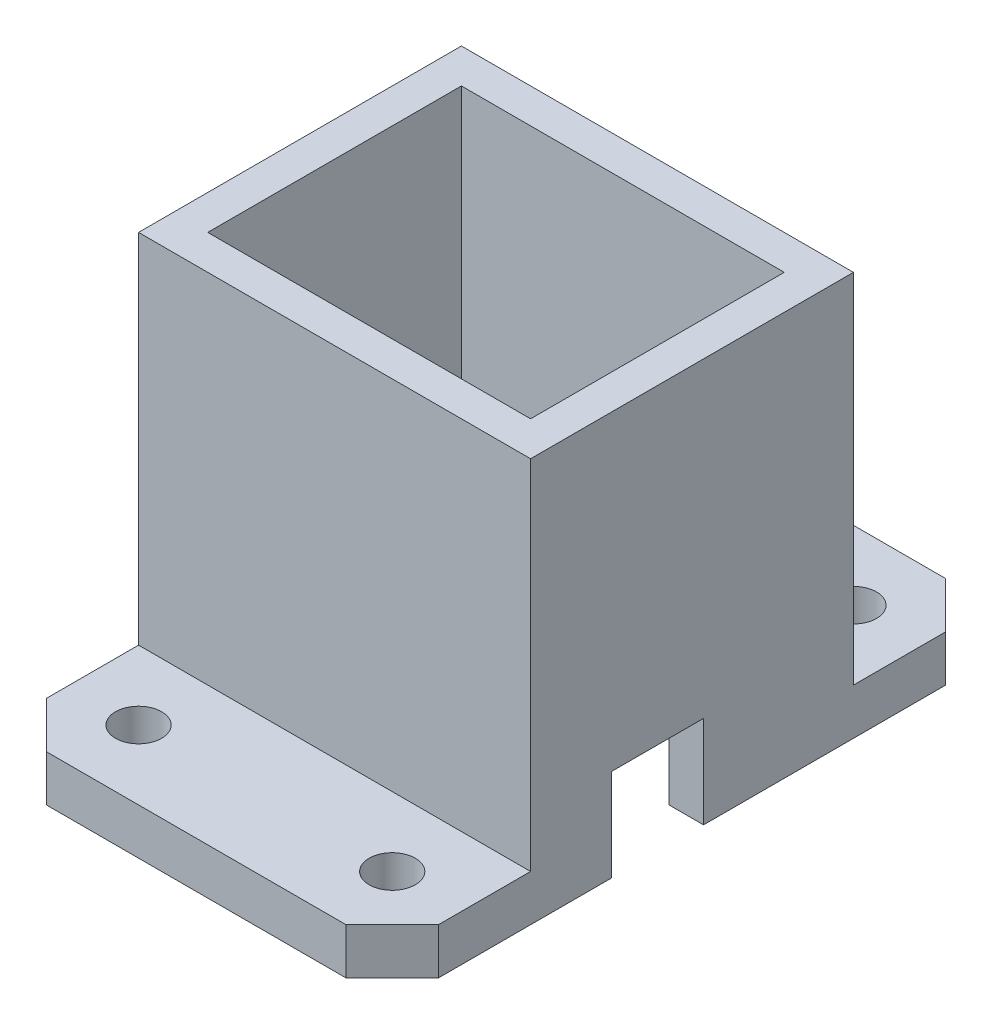
SolidWorks part; units mm, degrees
ref_plane "Front Plane" through (0, 0, 0) normal (0, 0, 1) x (1, 0, 0)
ref_plane "Top Plane" through (0, 0, 0) normal (0, 1, 0) x (1, 0, 0)
ref_plane "Right Plane" through (0, 0, 0) normal (1, 0, 0) x (0, 0, -1)
sketch "Sketch1" plane through (0, 0, 0) normal (0, 1, 0) x (1, 0, 0)
  line L1 (-14, -11) -> (14, -11)
  line L2 (-14, -11) -> (-14, 11)
  line L3 (-14, 11) -> (14, 11)
  line L4 (14, -11) -> (14, 11)
  line L5 (-14, -11) -> (14, 11) construction
  line L6 (-14, 11) -> (14, -11) construction
  line L7 (-17, -14) -> (17, -14)
  line L8 (-17, -14) -> (-17, 14)
  line L9 (-17, 14) -> (17, 14)
  line L10 (17, -14) -> (17, 14)
  line L11 (-17, -14) -> (17, 14) construction
  line L12 (-17, 14) -> (17, -14) construction
  point P0 (0, 0)
  point P5 (0, 0)
  dimension "D1" = 28
  dimension "D2" = 22
  dimension "D3" = 28
  dimension "D4" = 34
extrude "Boss-Extrude1" add sketch "Sketch1" along normal blind 35
sketch "Sketch2" plane through (-17, 0, 0) normal (-1, 0, 0) x (0, 0, 1)
  line L0 (-14, 0) -> (14, 0) construction
  line L1 (7, 0) -> (-1, 0)
  line L2 (7, 0) -> (7, 8)
  line L3 (7, 8) -> (-1, 8)
  line L4 (-1, 0) -> (-1, 8)
  line L5 (14, 35) -> (14, 0) construction
  dimension "D1" = 8
  dimension "D2" = 8
  dimension "D3" = 7
extrude "Cut-Extrude1" cut sketch "Sketch2" against normal blind 35
sketch "Sketch3" plane through (0, 0, 14) normal (0, 0, 1) x (1, 0, 0)
  line L0 (17, 35) -> (17, 0) construction
  line L1 (-17, 0) -> (17, 0)
  line L2 (-17, 0) -> (-17, 4)
  line L3 (-17, 4) -> (17, 4)
  line L4 (17, 0) -> (17, 4)
  dimension "D1" = 4
extrude "Boss-Extrude2" add sketch "Sketch3" along normal blind 12
sketch "Sketch4" plane through (0, 0, -14) normal (0, 0, -1) x (-1, 0, 0)
  line L0 (17, 35) -> (17, 0) construction
  line L1 (-17, 0) -> (17, 0)
  line L2 (-17, 0) -> (-17, 4)
  line L3 (-17, 4) -> (17, 4)
  line L4 (17, 0) -> (17, 4)
  dimension "D1" = 4
extrude "Boss-Extrude3" add sketch "Sketch4" along normal blind 12
chamfer "Chamfer1" distance 4 angle 45 4 edges at (-17, 2, 26) (-17, 2, -26) (17, 2, -26) (17, 2, 26)
sketch "Sketch5" plane through (0, 4, 0) normal (0, 1, 0) x (1, 0, 0)
  line L0 (13, -26) -> (-13, -26) construction
  line L1 (-17, -22) -> (-17, -14) construction
  line L2 (17, -22) -> (17, -14) construction
  line L3 (-13, 26) -> (13, 26) construction
  line L4 (-17, 22) -> (-17, 14) construction
  line L5 (17, 22) -> (17, 14) construction
  circle A0 centre (-11, -20) radius 2
  circle A1 centre (11, -20) radius 2
  circle A2 centre (-11, 20) radius 2
  circle A3 centre (11, 20) radius 2
  dimension "D1" = 4
  dimension "D2" = 4
  dimension "D3" = 4
  dimension "D4" = 4
  dimension "D5" = 6
  dimension "D6" = 6
  dimension "D7" = 6
  dimension "D8" = 6
  dimension "D9" = 6
  dimension "D10" = 6
  dimension "D11" = 6
  dimension "D12" = 6
extrude "Cut-Extrude2" cut sketch "Sketch5" against normal blind 4
